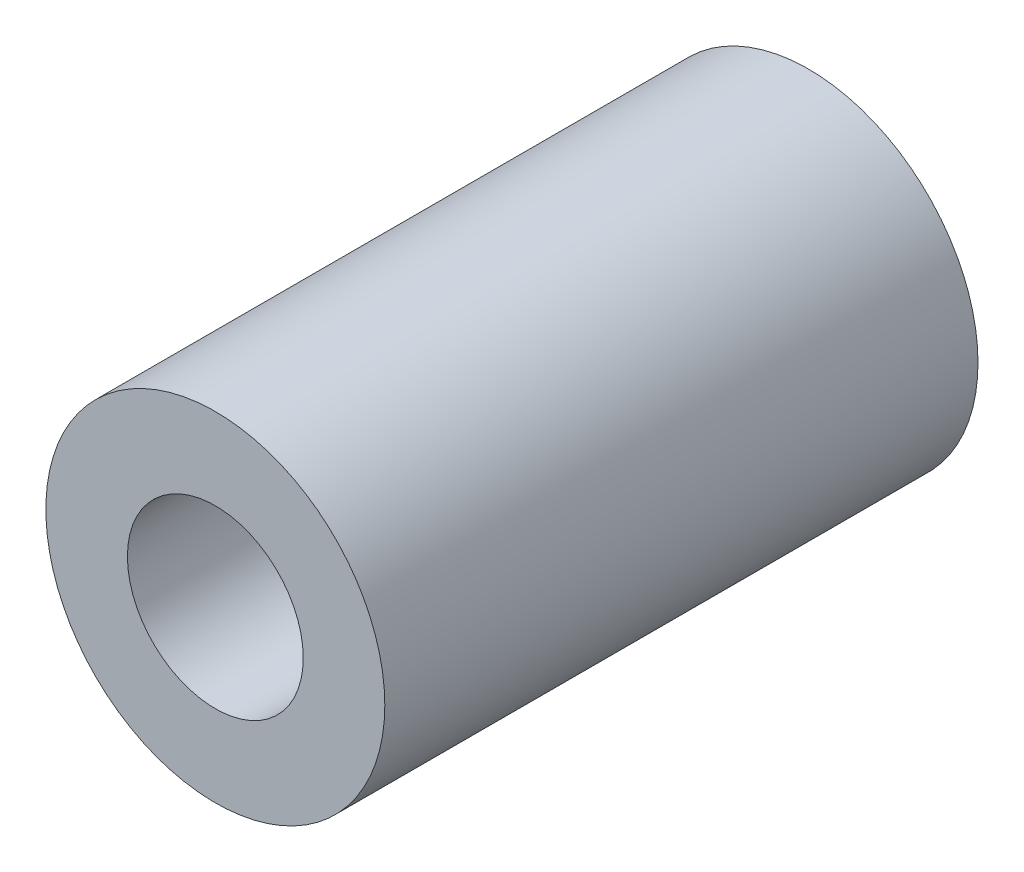
SolidWorks part; units mm, degrees
ref_plane "Front Plane" through (0, 0, 0) normal (0, 0, 1) x (1, 0, 0)
ref_plane "Top Plane" through (0, 0, 0) normal (0, 1, 0) x (1, 0, 0)
ref_plane "Right Plane" through (0, 0, 0) normal (1, 0, 0) x (0, 0, -1)
sketch "Sketch1" plane through (0, 0, 0) normal (0, 0, 1) x (1, 0, 0)
  circle A0 centre (0, 0) radius 4.15
  circle A3 centre (0, 0) radius 8
  dimension "D2" = 16
extrude "Boss-Extrude1" add sketch "Sketch1" along normal blind 28
